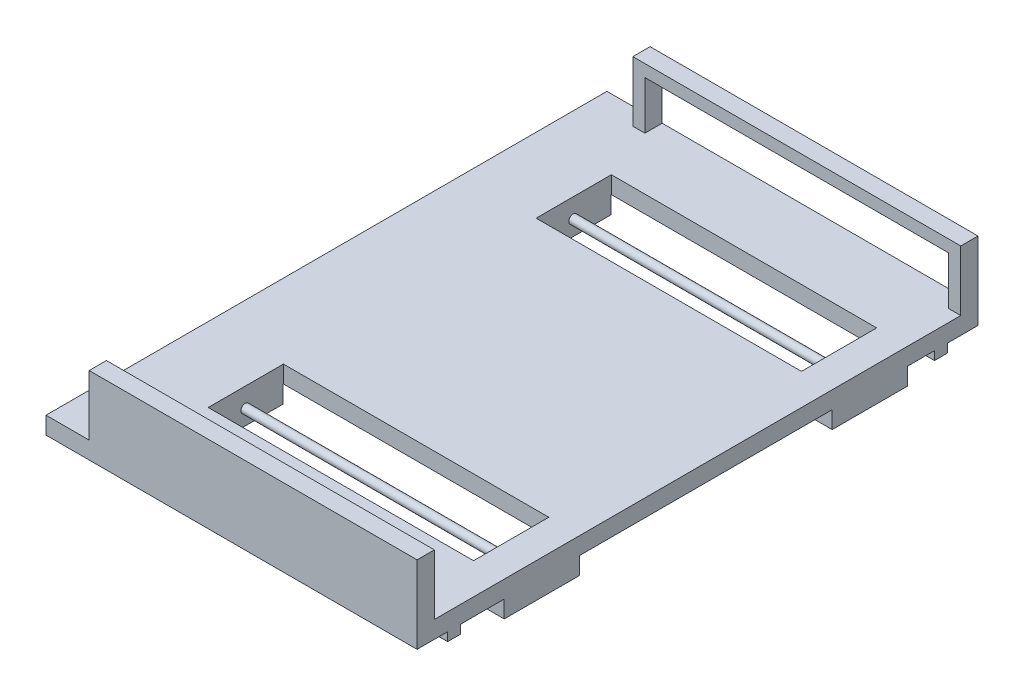
SolidWorks part; units mm, degrees
ref_plane "Front Plane" through (0, 0, 0) normal (0, 0, 1) x (1, 0, 0)
ref_plane "Top Plane" through (0, 0, 0) normal (0, 1, 0) x (1, 0, 0)
ref_plane "Right Plane" through (0, 0, 0) normal (1, 0, 0) x (0, 0, -1)
sketch "Sketch1" plane through (0, 0, 0) normal (1, 0, 0) x (0, 0, -1)
  line L0 (-162.5, 30.0674) -> (-162.5, -4.8577)
  line L1 (-162.5, -4.8577) -> (162.5, -4.8577)
  line L2 (-162.5, -4.8577) -> (-162.5, -14.8577)
  line L3 (-162.5, -14.8577) -> (162.5, -14.8577)
  line L4 (162.5, -4.8577) -> (162.5, -14.8577)
  line L6 (162.5, -4.8577) -> (162.5, 30.0674)
  line L7 (162.5, 30.0674) -> (152.5, 30.0674)
  line L8 (152.5, -4.8577) -> (152.5, 30.0674)
  line L10 (-162.5, -4.8577) -> (-162.5, 30.0674)
  line L11 (-162.5, 30.0674) -> (-152.5, 30.0674)
  line L12 (-152.5, -4.8577) -> (-152.5, 30.0674)
  line L13 (162.5, 30.0674) -> (162.5, -4.8577)
  point P10 (0, -14.8577)
  dimension "D1" = 325
  dimension "D2" = 10
  dimension "D3" = 10
  dimension "D4" = 10
extrude "Boss-Extrude1" add sketch "Sketch1" along normal blind 190 contours L4 L1 L2 L3 | L1 L12 L11 L0 | L8 L1 L6 L7
sketch "Sketch2" plane through (0, -14.8577, 0) normal (0, -1, 0) x (1, 0, 0)
  line L0 (0, 162.5) -> (0, -162.5) construction
  line L1 (0, 144.7804) -> (190, 144.7804)
  line L2 (0, 144.7804) -> (0, 137.2804)
  line L3 (0, 137.2804) -> (190, 137.2804)
  line L4 (190, 144.7804) -> (190, 137.2804)
  line L5 (190, 162.5) -> (190, -162.5) construction
  line L6 (190, 162.5) -> (0, 162.5) construction
  line L7 (190, -162.5) -> (0, -162.5) construction
  line L8 (0, -137.28) -> (190, -137.28)
  line L9 (0, -137.28) -> (0, -144.78)
  line L10 (0, -144.78) -> (190, -144.78)
  line L11 (190, -137.28) -> (190, -144.78)
  dimension "D1" = 7.5
  dimension "D2" = 17.7196
  dimension "D3" = 17.72
  dimension "D4" = 7.5
extrude "Boss-Extrude2" add sketch "Sketch2" along normal blind 5
sketch "Sketch6" plane through (0, 0, 0) normal (-1, 0, 0) x (0, 0, 1)
  line L0 (137.2804, -14.8577) -> (-137.28, -14.8577) construction
  line L1 (68.4049, -14.8577) -> (112.0049, -14.8577)
  line L2 (68.4049, -14.8577) -> (68.4049, -24.8577)
  line L3 (68.4049, -24.8577) -> (112.0049, -24.8577)
  line L4 (112.0049, -14.8577) -> (112.0049, -24.8577)
  dimension "D1" = 10
  dimension "D2" = 43.6
extrude "Boss-Extrude4" add sketch "Sketch6" against normal through all
sketch "Sketch3" plane through (0, -14.8577, 0) normal (0, -1, 0) x (1, 0, 0)
  line L0 (0, 137.2804) -> (0, 112.0049) construction
  line L1 (18.125, 111.6547) -> (171.875, 111.6547)
  line L2 (18.125, 111.6547) -> (18.125, 68.0578)
  line L3 (18.125, 68.0578) -> (171.875, 68.0578)
  line L4 (171.875, 111.6547) -> (171.875, 68.0578)
  line L5 (190, 137.2804) -> (190, 112.0049) construction
  dimension "D1" = 18.125
  dimension "D2" = 18.125
  dimension "D3" = 153.75
extrude "Cut-Extrude1" cut sketch "Sketch3" against normal through all both and the other way through all
sketch "Sketch4" plane through (171.875, 0, 0) normal (-1, 0, 0) x (0, 0, 1)
  line L0 (112.0049, -24.8577) -> (112.0049, -14.8577) construction
  line L1 (68.4049, -14.8577) -> (68.4049, -24.8577) construction
  circle A0 centre (90.2073, -15.9873) radius 2.5
  point P2 (89.5396, -20.0365)
  point P7 (90.2073, -15.9873)
  dimension "D1" = 5
  dimension "D2" = 21.7976
  dimension "D3" = 21.8024
extrude "Boss-Extrude3" add sketch "Sketch4" along normal through all
pattern_linear "LPattern1" count 2 spacing 190 along (0, 0, -1) of "Boss-Extrude4", "Cut-Extrude1", "Boss-Extrude3"
sketch "Sketch7" plane through (0, 0, 152.5) normal (0, 0, -1) x (-1, 0, 0)
  line L1 (-183, -4.8577) -> (-7, -4.8577)
  line L2 (-183, -4.8577) -> (-183, 23.0674)
  line L3 (-183, 23.0674) -> (-7, 23.0674)
  line L4 (-7, -4.8577) -> (-7, 23.0674)
  line L5 (-190, 30.0674) -> (-190, -14.8577) construction
  line L6 (0, 30.0674) -> (0, -14.8577) construction
  line L7 (-190, 30.0674) -> (0, 30.0674) construction
  line L11 (-190, -4.8577) -> (0, -4.8577) construction
  dimension "D1" = 7
  dimension "D2" = 7
  dimension "D3" = 7
extrude "Cut-Extrude5" cut sketch "Sketch7" along normal up to surface (315 mm away) up to face at (95, 7.6049, -162.5)
sketch "Sketch8" plane through (0, 0, -162.5) normal (0, 0, -1) x (-1, 0, 0)
  line L0 (0, 30.0674) -> (0, -14.8577) construction
  line L1 (0, -4.8577) -> (25, -4.8577)
  line L2 (0, -4.8577) -> (0, -14.8577)
  line L3 (0, -14.8577) -> (25, -14.8577)
  line L4 (25, -4.8577) -> (25, -14.8577)
  line L5 (-190, -4.8577) -> (0, -4.8577) construction
  dimension "D1" = 25
extrude "Boss-Extrude6" add sketch "Sketch8" against normal up to surface (325 mm away) up to face at (95, 7.6049, 162.5)
